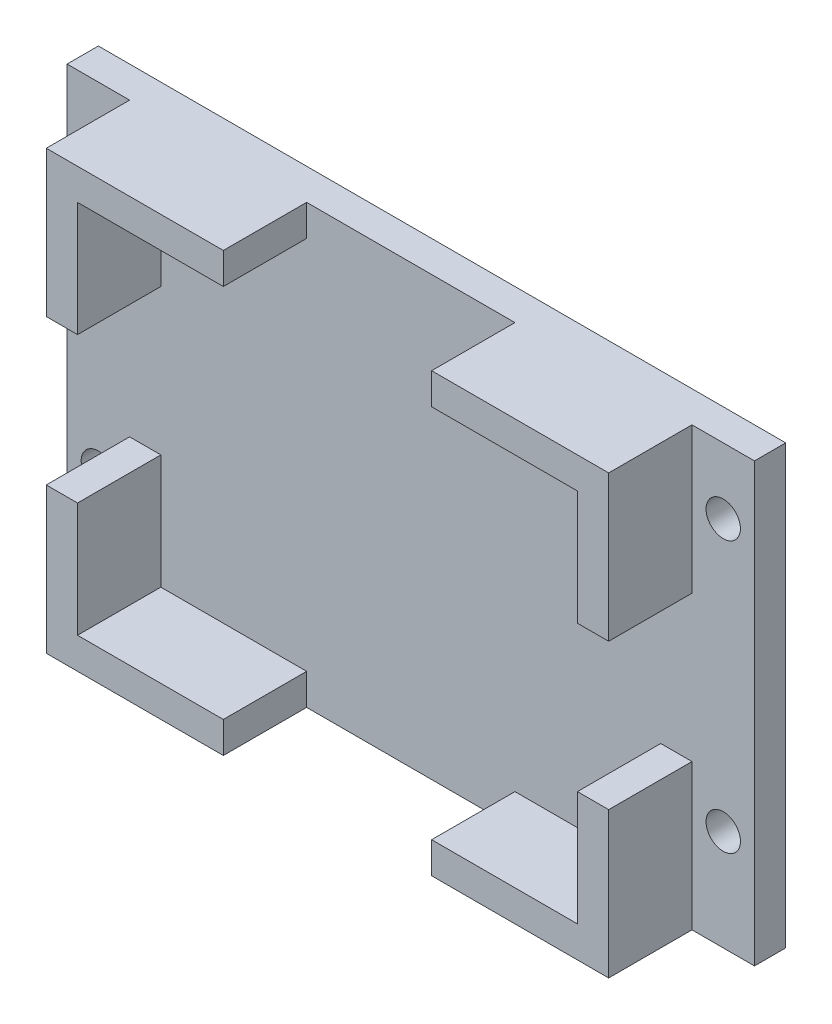
SolidWorks part; units mm, degrees
ref_plane "前视基准面" through (0, 0, 0) normal (0, 0, 1) x (1, 0, 0)
ref_plane "上视基准面" through (0, 0, 0) normal (0, 1, 0) x (1, 0, 0)
ref_plane "右视基准面" through (0, 0, 0) normal (1, 0, 0) x (0, 0, -1)
sketch "草图1" plane through (0, 0, 0) normal (0, 0, 1) x (1, 0, 0)
  line L0 (0, 0) -> (0, 21)
  line L1 (-27, 21) -> (27, 21)
  line L2 (-27, 21) -> (-27, -21)
  line L3 (-27, -21) -> (27, -21)
  line L4 (27, 21) -> (27, -21)
  line L5 (-27, 21) -> (27, -21) construction
  line L6 (-27, -21) -> (27, 21) construction
  line L7 (-24, 18) -> (24, 18)
  line L8 (-24, 18) -> (-24, -18)
  line L9 (-24, -18) -> (24, -18)
  line L10 (24, 18) -> (24, -18)
  line L11 (-24, 18) -> (24, -18) construction
  line L12 (-24, -18) -> (24, 18) construction
  line L13 (27, 21) -> (33, 21)
  line L14 (27, 21) -> (27, -21)
  line L15 (27, -21) -> (33, -21)
  line L16 (33, 21) -> (33, -21)
  line L17 (-27, 21) -> (-33, 21)
  line L18 (-27, 21) -> (-27, -21)
  line L19 (-27, -21) -> (-33, -21)
  line L20 (-33, 21) -> (-33, -21)
  line L21 (-30, 21) -> (-30, 14.6832)
  line L22 (-30, 14.6832) -> (-30, -11.3168)
  circle A0 centre (-30, 14.6832) radius 1.65
  circle A1 centre (-30, -11.3168) radius 1.65
  circle A2 centre (30, -11.3168) radius 1.65
  circle A3 centre (30, 14.6832) radius 1.65
  point P0 (0, 0)
  point P6 (0, 0)
  dimension "D1" = 42
  dimension "D3" = 3.3
  dimension "D4" = 3.3
  dimension "D2" = 6
extrude "凸台-拉伸3" add sketch "草图1" along normal blind 3
sketch "草图3" plane through (0, 0, 3) normal (0, 0, 1) x (1, 0, 0)
  line L1 (-24, 18) -> (24, 18)
  line L2 (-24, 18) -> (-24, -18)
  line L3 (-24, -18) -> (24, -18)
  line L4 (24, 18) -> (24, -18)
  line L5 (-24, 18) -> (24, -18) construction
  line L6 (-24, -18) -> (24, 18) construction
  line L7 (-27, 21) -> (27, 21)
  line L8 (-27, 21) -> (-27, -21)
  line L9 (-27, -21) -> (27, -21)
  line L10 (27, 21) -> (27, -21)
  line L11 (-27, 21) -> (27, -21) construction
  line L12 (-27, -21) -> (27, 21) construction
  point P0 (0, 0)
  point P6 (0, 0)
extrude "凸台-拉伸4" add sketch "草图3" along normal blind 8
sketch "草图4" plane through (0, -21, 0) normal (0, -1, 0) x (1, 0, 0)
  line L0 (-10, 11) -> (-10, 3)
  line L1 (-27, 11) -> (27, 11) construction
  line L2 (-10, 3) -> (10, 3)
  line L3 (10, 3) -> (10, 11)
  line L4 (0, 0) -> (0, 31.1009) construction
  line L5 (33, 0) -> (-33, 0) construction
  line L6 (33, 3) -> (27, 3) construction
  point P10 (0, 0)
  dimension "D1" = 20
extrude "切除-拉伸1" cut sketch "草图4" against normal through all and the other way through all
sketch "草图5" plane through (-27, 0, 0) normal (-1, 0, 0) x (0, 0, 1)
  line L0 (0, 0) -> (26.7504, 0) construction
  line L1 (11, 7) -> (3, 7)
  line L2 (11, 21) -> (11, -21) construction
  line L3 (3, 21) -> (3, -21) construction
  line L4 (3, 7) -> (3, -7)
  line L5 (3, 21) -> (3, -21) construction
  line L6 (3, -7) -> (11, -7)
  line L7 (11, 7) -> (11, -7)
  dimension "D1" = 14
extrude "切除-拉伸2" cut sketch "草图5" against normal through all
